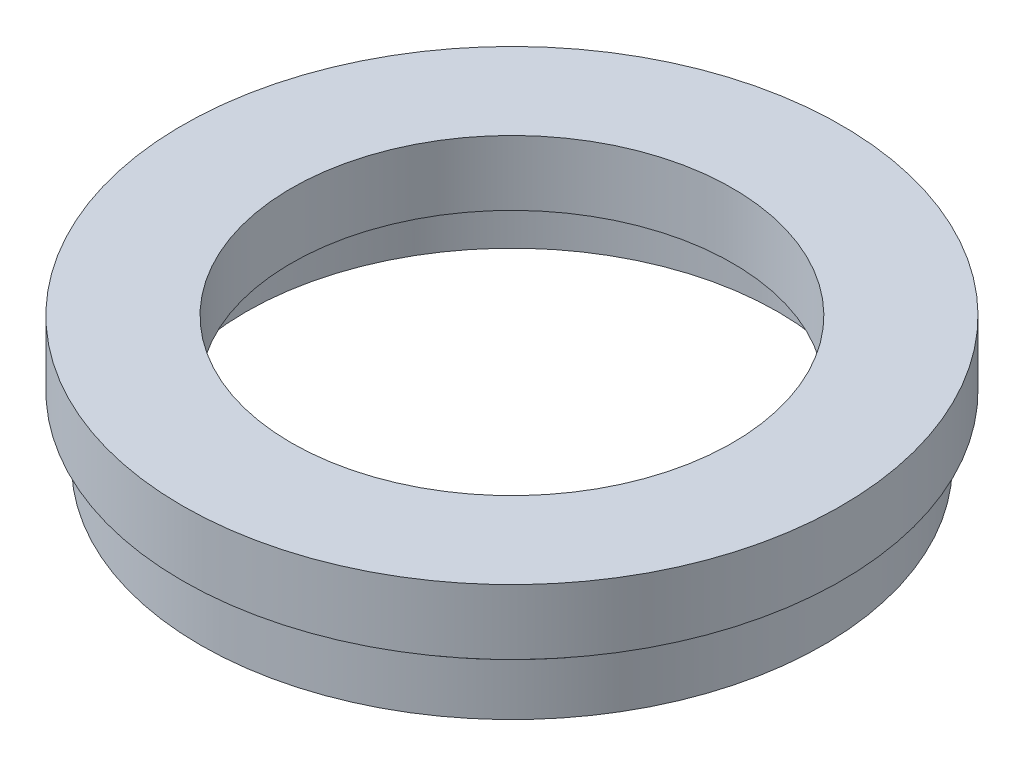
SolidWorks part; units mm, degrees
ref_plane "前视基准面" through (0, 0, 0) normal (0, 0, 1) x (1, 0, 0)
ref_plane "上视基准面" through (0, 0, 0) normal (0, 1, 0) x (1, 0, 0)
ref_plane "右视基准面" through (0, 0, 0) normal (1, 0, 0) x (0, 0, -1)
sketch "草图1" plane through (0, 0, 0) normal (0, 0, 1) x (1, 0, 0)
  line L0 (0, 17.4193) -> (0, -25.7883) construction
  line L1 (20.5, 0) -> (20.5, 4)
  line L2 (20.5, 4) -> (21.1, 4)
  line L3 (21.1, 4) -> (21.1, 5)
  line L4 (21.1, 5) -> (17, 5)
  line L5 (17, 5) -> (17, 10)
  line L6 (17, 10) -> (25.4, 10)
  line L7 (20.5, 0) -> (24, 0)
  line L8 (24, 0) -> (24, 4)
  line L9 (24, 4) -> (23.5, 4)
  line L10 (23.5, 4) -> (23.5, 5)
  line L11 (23.5, 5) -> (25.4, 5)
  line L12 (25.4, 5) -> (25.4, 10)
  dimension "D1" = 20.5
  dimension "D2" = 21.1
  dimension "D3" = 17
  dimension "D4" = 24
  dimension "D5" = 23.5
  dimension "D6" = 25.4
  dimension "D7" = 1
  dimension "D8" = 1
  dimension "D9" = 5
  dimension "D10" = 10
revolve "旋转1" add sketch "草图1" angle 360 about L0
cosmetic thread "装饰螺纹线1" parameters "D1"=5, "D2"=35
cosmetic thread "装饰螺纹线2" parameters "D1"=5, "D2"=42
cosmetic thread "装饰螺纹线3" parameters "D1"=4, "D2"=47
